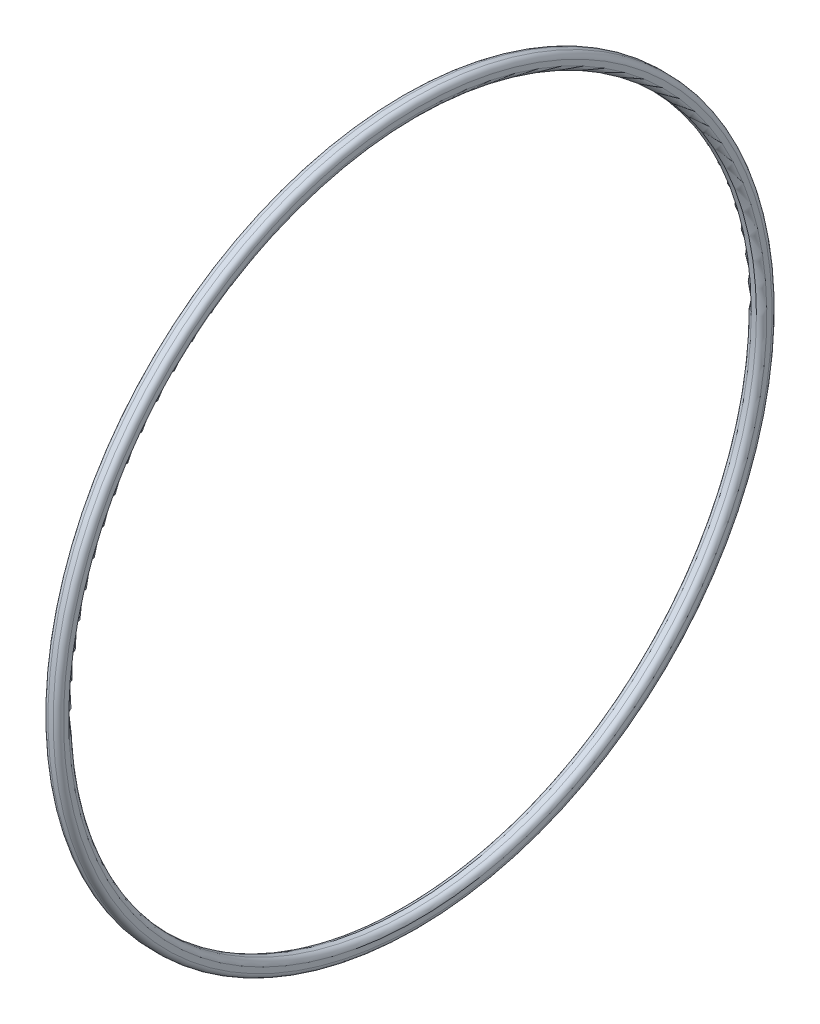
SolidWorks part; units mm, degrees
material "Gomma siliconata"
ref_plane "Piano frontale" through (0, 0, 0) normal (0, 0, 1) x (1, 0, 0)
ref_plane "Piano superiore" through (0, 0, 0) normal (0, 1, 0) x (1, 0, 0)
ref_plane "Piano destro" through (0, 0, 0) normal (1, 0, 0) x (0, 0, -1)
sketch "Schizzo1" plane through (0, 0, 0) normal (0, 0, 1) x (1, 0, 0)
  line L0 (0, 0) -> (0, -67.75) construction
  line L1 (0, -67.75) -> (-69.175, -67.75) construction
  line L3 (-0.4998, -1.5) -> (0.4998, -1.5)
  line L4 (-1.4998, -0.5) -> (-1.4998, 0.5)
  line L5 (-0.4998, 1.5) -> (0.4998, 1.5)
  line L6 (1.4998, -0.5) -> (1.4998, 0.5)
  line L7 (-1.4998, -1.5) -> (1.4998, 1.5) construction
  line L8 (-1.4998, 1.5) -> (1.4998, -1.5) construction
  arc A1 (0.4998, 1.5) -> (1.4998, 0.5) centre (0.4998, 0.5) cw
  arc A2 (1.4998, -0.5) -> (0.4998, -1.5) centre (0.4998, -0.5) cw
  arc A3 (-0.4998, -1.5) -> (-1.4998, -0.5) centre (-0.4998, -0.5) cw
  arc A4 (-0.4998, 1.5) -> (-1.4998, 0.5) centre (-0.4998, 0.5) ccw
  dimension "D1" = 1
  dimension "D2" = 67.75
  dimension "D3" = 2.9996
  dimension "D4" = 3
revolve "Rivoluzione1" add sketch "Schizzo1" angle 360 about L1
